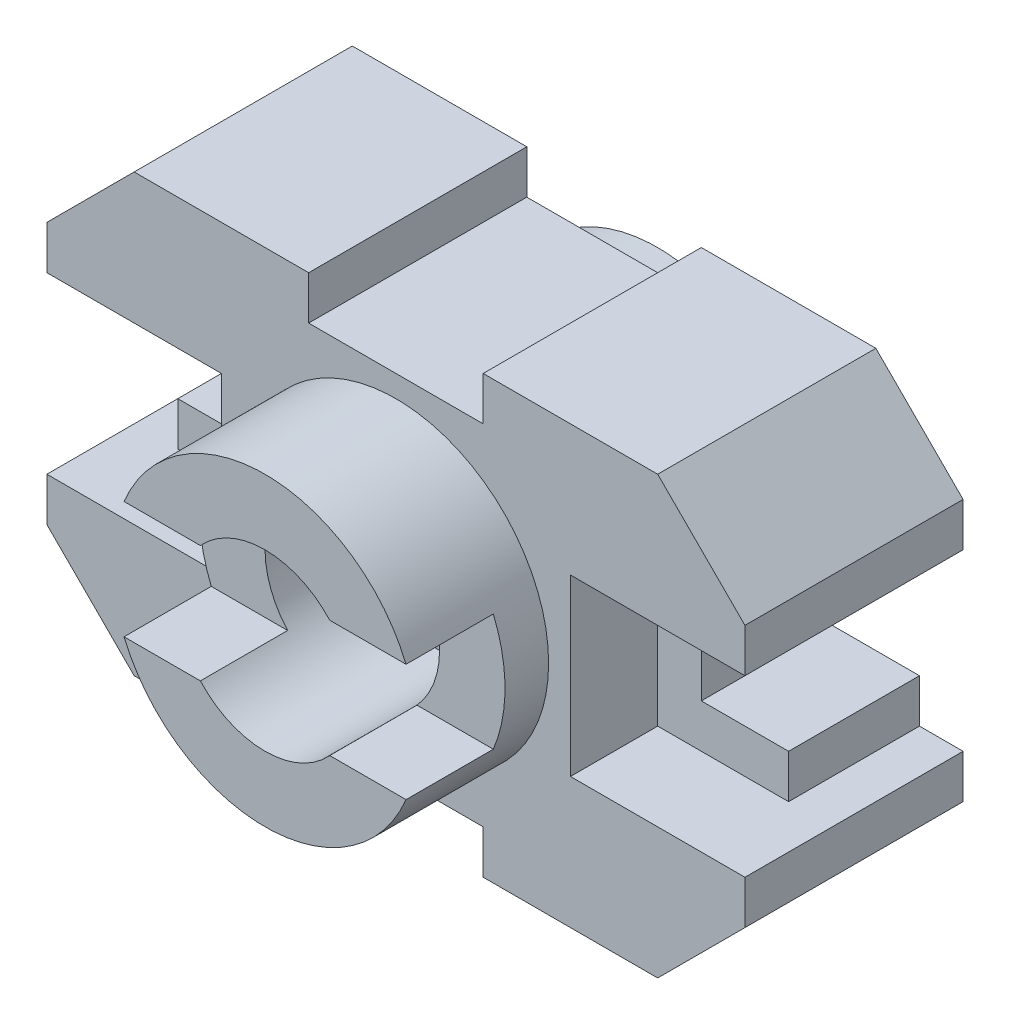
SolidWorks part; units mm, degrees
ref_plane "Front Plane" through (0, 0, 0) normal (0, 0, 1) x (1, 0, 0)
ref_plane "Top Plane" through (0, 0, 0) normal (0, 1, 0) x (1, 0, 0)
ref_plane "Right Plane" through (0, 0, 0) normal (1, 0, 0) x (0, 0, -1)
sketch "Sketch1" plane through (0, 0, 0) normal (0, 0, 1) x (1, 0, 0)
  line L0 (-60, 0) -> (-60, -5)
  line L1 (-60, -5) -> (-50, -15)
  line L2 (-50, -15) -> (-30, -15)
  line L3 (-30, -15) -> (-30, -10)
  line L4 (-30, -10) -> (-10, -10)
  line L5 (-10, -10) -> (-10, -15)
  line L6 (-10, -15) -> (10, -15)
  line L7 (10, -15) -> (20, -5)
  line L8 (20, -5) -> (20, 0)
  line L9 (20, 0) -> (0, 0)
  line L10 (0, 0) -> (0, 20)
  line L11 (0, 20) -> (20, 20)
  line L12 (20, 20) -> (20, 25)
  line L13 (20, 25) -> (10, 35)
  line L14 (10, 35) -> (-10, 35)
  line L15 (-10, 35) -> (-10, 30)
  line L16 (-10, 30) -> (-30, 30)
  line L17 (-30, 30) -> (-30, 35)
  line L18 (-30, 35) -> (-50, 35)
  line L19 (-50, 35) -> (-60, 25)
  line L20 (-60, 25) -> (-60, 20)
  line L21 (-60, 20) -> (-40, 20)
  line L22 (-40, 20) -> (-40, 0)
  line L23 (-40, 0) -> (-60, 0)
  dimension "D1" = 20
  dimension "D2" = 5
  dimension "D3" = 5
  dimension "D4" = 20
  dimension "D5" = 20
  dimension "D6" = 20
  dimension "D7" = 20
  dimension "D8" = 5
  dimension "D9" = 5
  dimension "D10" = 20
  dimension "D11" = 10
  dimension "D12" = 10
  dimension "D13" = 10
  dimension "D14" = 10
  dimension "D15" = 10
  dimension "D16" = 10
  dimension "D17" = 10
  dimension "D18" = 5
  dimension "D19" = 5
  dimension "D20" = 20
  dimension "D21" = 20
  dimension "D22" = 20
  dimension "D23" = 20
  dimension "D24" = 20
  dimension "D25" = 5
extrude "Boss-Extrude1" add sketch "Sketch1" along normal blind 25
sketch "Sketch2" plane through (0, 0, 0) normal (0, 0, -1) x (-1, 0, 0)
  line L0 (55, 20) -> (40, 20)
  line L1 (60, 20) -> (40, 20) construction
  line L2 (40, 20) -> (40, 0)
  line L3 (40, 0) -> (55, 0)
  line L4 (40, 0) -> (60, 0) construction
  line L5 (55, 0) -> (55, 5)
  line L6 (55, 5) -> (45, 5)
  line L7 (45, 5) -> (45, 15)
  line L8 (45, 15) -> (55, 15)
  line L9 (55, 15) -> (55, 20)
  line L10 (-15, 15) -> (-15, 20)
  line L11 (0, 20) -> (-20, 20) construction
  line L12 (-15, 20) -> (0, 20)
  line L13 (0, 20) -> (0, 0)
  line L14 (0, 0) -> (-15, 0)
  line L15 (-20, 0) -> (0, 0) construction
  line L16 (-15, 0) -> (-15, 5)
  line L17 (-15, 5) -> (-5, 5)
  line L18 (-5, 5) -> (-5, 15)
  line L19 (-5, 15) -> (-15, 15)
  dimension "D1" = 5
  dimension "D2" = 5
  dimension "D3" = 10
  dimension "D4" = 10
  dimension "D5" = 5
  dimension "D6" = 5
  dimension "D7" = 5
  dimension "D8" = 10
  dimension "D9" = 10
  dimension "D10" = 5
extrude "Boss-Extrude5" add sketch "Sketch2" against normal blind 15
sketch "Sketch3" plane through (0, 0, 25) normal (0, 0, 1) x (1, 0, 0)
  line L0 (0, 0) -> (0, 20) construction
  line L1 (-10, 30) -> (-30, 30) construction
  circle A0 centre (-20, 10) radius 17.5
  dimension "D1" = 35
  dimension "D2" = 20
  dimension "D3" = 20
extrude "Boss-Extrude6" add sketch "Sketch3" along normal blind 15
sketch "Sketch4" plane through (0, 0, 40) normal (0, 0, 1) x (1, 0, 0)
  circle A0 centre (-20, 10) radius 10
  dimension "D1" = 20
extrude "Cut-Extrude1" cut sketch "Sketch4" against normal blind 20
sketch "Sketch5" plane through (0, 0, 20) normal (0, 0, 1) x (1, 0, 0)
  circle A0 centre (-20, 10) radius 7.5
  point P0 (-20, 10)
  dimension "D1" = 15
extrude "Cut-Extrude2" cut sketch "Sketch5" against normal blind 80
sketch "Sketch6" plane through (0, 0, 40) normal (0, 0, 1) x (1, 0, 0)
  line L0 (-36.1607, 16.7143) -> (-27.4107, 16.7143)
  line L1 (-36.1607, 3.2857) -> (-27.4107, 3.2857)
  line L2 (-12.5893, 16.7143) -> (-3.8393, 16.7143)
  line L3 (-12.5893, 3.2857) -> (-3.8393, 3.2857)
  circle A0 centre (-20, 10) radius 17.5 construction
  circle A1 centre (-20, 10) radius 10 construction
  circle A2 centre (-20, 10) radius 10 construction
  arc A3 (-27.4107, 3.2857) -> (-27.4107, 16.7143) centre (-20, 10) cw
  arc A4 (-36.1607, 3.2857) -> (-36.1607, 16.7143) centre (-20, 10) cw
  circle A5 centre (-20, 10) radius 17.5 construction
  arc A6 (-12.5893, 3.2857) -> (-12.5893, 16.7143) centre (-20, 10) ccw
  arc A7 (-3.8393, 3.2857) -> (-3.8393, 16.7143) centre (-20, 10) ccw
  dimension "D1" = 8.75
  dimension "D2" = 10
  dimension "D3" = 17.5
  dimension "D4" = 10
  dimension "D5" = 17.5
extrude "Cut-Extrude3" cut sketch "Sketch6" against normal blind 10
sketch "Sketch7" plane through (0, 0, 0) normal (0, 0, -1) x (-1, 0, 0)
  circle A0 centre (20, 10) radius 17.5
  circle A1 centre (20, 10) radius 17.5 construction
extrude "Boss-Extrude7" add sketch "Sketch7" along normal blind 5
sketch "Sketch8" plane through (0, 0, -5) normal (0, 0, -1) x (-1, 0, 0)
  circle A0 centre (20, 10) radius 7.5
  dimension "D1" = 15
extrude "Cut-Extrude4" cut sketch "Sketch8" against normal blind 315
